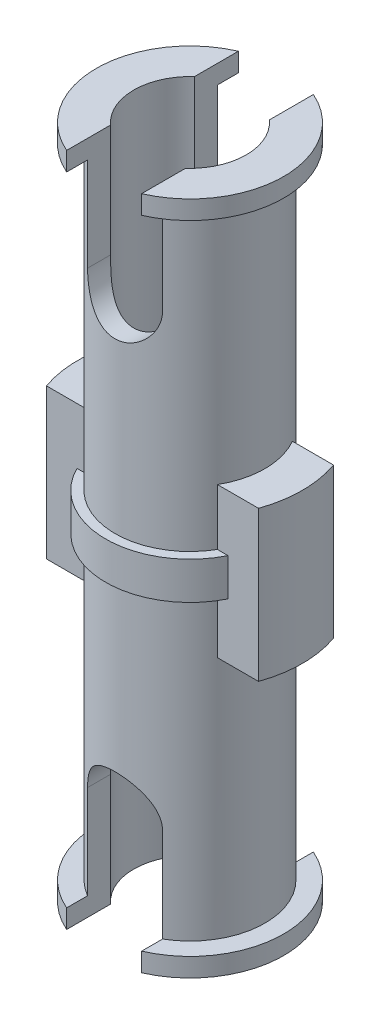
SolidWorks part; units mm, degrees
material "PBT General Purpose"
ref_plane "Front Plane" through (0, 0, 0) normal (0, 0, 1) x (1, 0, 0)
ref_plane "Top Plane" through (0, 0, 0) normal (0, 1, 0) x (1, 0, 0)
ref_plane "Right Plane" through (0, 0, 0) normal (1, 0, 0) x (0, 0, -1)
sketch "Sketch1" plane through (0, 0, 0) normal (0, 0, 1) x (1, 0, 0)
  line L0 (0, 9) -> (0, -9) construction
  line L1 (-2, 9) -> (0, 9)
  line L3 (-2, -9) -> (-2, 9)
  line L6 (-2, -9) -> (0, -9)
  line L7 (0, 9) -> (0, -9)
  line L9 (0, 9) -> (-2.5, 9)
  line L10 (0, 9) -> (0, 8.5)
  line L11 (0, 8.5) -> (-2.5, 8.5)
  line L12 (-2.5, 9) -> (-2.5, 8.5)
  line L13 (0, -9) -> (-2.5, -9)
  line L14 (0, -9) -> (0, -8.5)
  line L15 (0, -8.5) -> (-2.5, -8.5)
  line L16 (-2.5, -9) -> (-2.5, -8.5)
  line L17 (0, -0.5) -> (-2.25, -0.5)
  line L18 (0, -0.5) -> (0, 0.5)
  line L19 (0, 0.5) -> (-2.25, 0.5)
  line L20 (-2.25, -0.5) -> (-2.25, 0.5)
  point P3 (0, 0)
  point P16 (0, 0)
  dimension "D1" = 18
  dimension "D2" = 2
  dimension "D3" = 2.5
  dimension "D4" = 0.5
  dimension "D5" = 1
  dimension "D6" = 2.25
revolve "Revolve5" add sketch "Sketch1" angle 360 about L0
sketch "Sketch3" plane through (0, 0, 0) normal (0, 0, 1) x (1, 0, 0)
  line L0 (2.25, 0) -> (-2.25, 0) construction
  line L1 (2.25, -0.5) -> (2.25, 0.5) construction
  line L2 (-2.25, 0.5) -> (-2.25, -0.5) construction
  line L4 (-3, -2) -> (3, -2)
  line L5 (-3, -2) -> (-3, 2)
  line L6 (-3, 2) -> (3, 2)
  line L7 (3, -2) -> (3, 2)
  line L8 (2, 0.5) -> (2, 8.5) construction
  point P13 (3, 0)
  dimension "D1" = 4
  dimension "D2" = 6
  dimension "D3" = 1
extrude "Boss-Extrude4" add sketch "Sketch3" along normal mid plane 2
sketch "Sketch5" plane through (0, 0, 0) normal (0, 0, 1) x (1, 0, 0)
  line L0 (-1, 9) -> (-1, 6)
  line L1 (2.5, 9) -> (-2.5, 9) construction
  line L2 (1, 6) -> (1, 9)
  line L3 (1, 9) -> (-1, 9)
  line L8 (-1, -9) -> (-1, -6)
  line L9 (-2.5, -9) -> (2.5, -9) construction
  line L10 (1, -6) -> (1, -9)
  line L11 (1, -9) -> (-1, -9)
  arc A0 (-1, 6) -> (1, 6) centre (0, 6) ccw
  arc A2 (-1, -6) -> (1, -6) centre (0, -6) cw
  dimension "D1" = 1
  dimension "D2" = 3
extrude "Cut-Extrude2" cut sketch "Sketch5" against normal through all both and the other way through all
sketch "Sketch6" plane through (0, 9, 0) normal (0, 1, 0) x (1, 0, 0)
  circle A0 centre (0, 0) radius 1.5
  dimension "D1" = 3
extrude "Cut-Extrude3" cut sketch "Sketch6" against normal up to surface (18 mm away) up to face at (-1.75, -9, 0)
sketch "Sketch7" plane through (0, 0, 0) normal (0, 1, 0) x (1, 0, 0)
  circle A0 centre (0, 0) radius 3
  dimension "D1" = 6
extrude "Cut-Extrude4" cut sketch "Sketch7" against normal through all both and the other way through all flip side to cut
